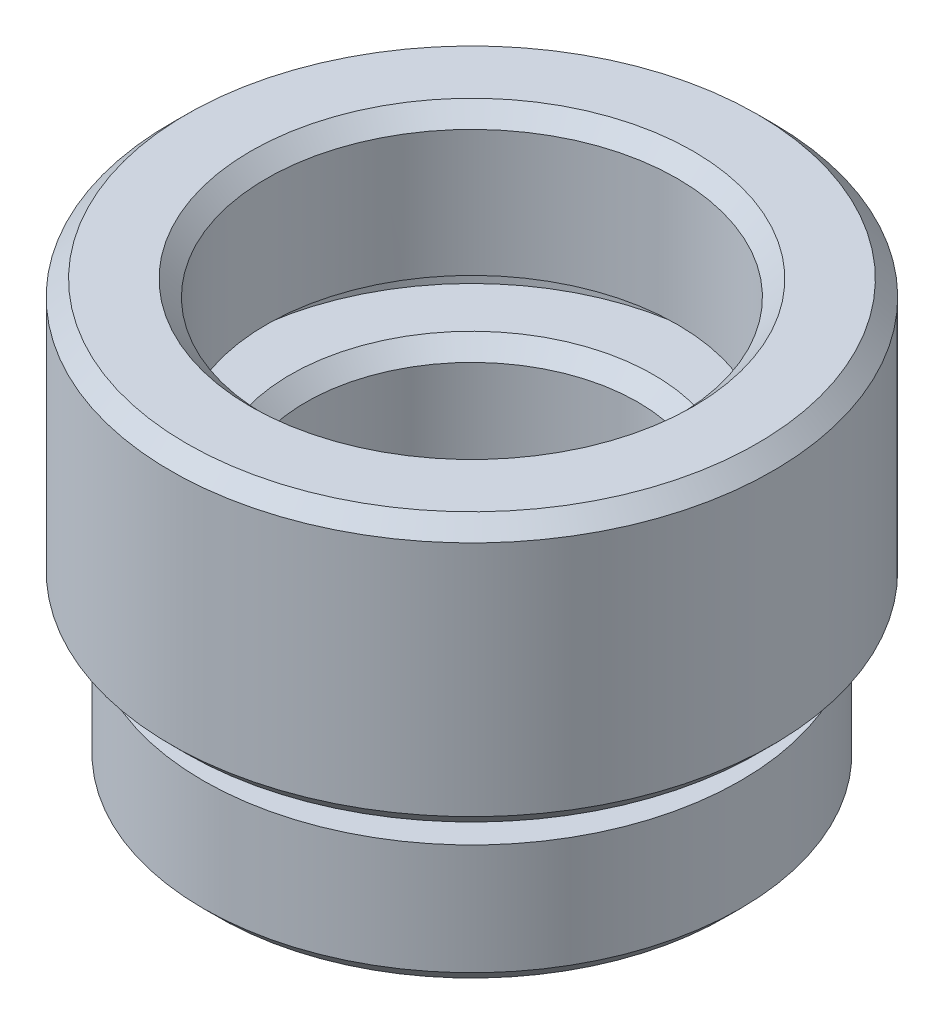
SolidWorks part; units mm, degrees
ref_plane "前视基准面" through (0, 0, 0) normal (0, 0, 1) x (1, 0, 0)
ref_plane "上视基准面" through (0, 0, 0) normal (0, 1, 0) x (1, 0, 0)
ref_plane "右视基准面" through (0, 0, 0) normal (1, 0, 0) x (0, 0, -1)
sketch "草图1" plane through (0, 0, 0) normal (0, 0, 1) x (1, 0, 0)
  line L0 (0, 0) -> (0, 51.3875) construction
  line L1 (4.5, 0) -> (4.5, 2)
  line L2 (4.5, 2) -> (5, 2)
  line L3 (5, 2) -> (5, 3.5)
  line L4 (5, 3.5) -> (6.35, 3.5)
  line L5 (6.35, 3.5) -> (6.35, 4.5)
  line L6 (6.35, 4.5) -> (5.25, 4.5)
  line L7 (5.25, 4.5) -> (5.25, 8)
  line L8 (5.25, 8) -> (7.6, 8)
  line L9 (4.5, 0) -> (8, 0)
  line L10 (7.6, 8) -> (7.6, 9)
  line L11 (7.6, 9) -> (6.5, 9)
  line L12 (6.5, 9) -> (6.5, 13.5)
  line L13 (6.5, 13.5) -> (9.025, 13.5)
  line L14 (0, 0) -> (5.8539, 0) construction
  line L15 (8.5, 0.5) -> (8.5, 4)
  line L16 (8.5, 4) -> (7, 4)
  line L17 (7, 4) -> (7, 5)
  line L18 (7, 5) -> (9.025, 5)
  line L19 (9.525, 5.5) -> (9.525, 13)
  line L20 (8, 0) -> (8.5, 0.5)
  line L21 (9.025, 5) -> (9.525, 5.5)
  line L22 (9.525, 13) -> (9.025, 13.5)
  point P13 (8.5, 0)
  point P22 (9.525, 5)
  point P24 (9.525, 13.5)
  dimension "D1" = 4.5
  dimension "D2" = 2
  dimension "D3" = 5
  dimension "D4" = 1.5
  dimension "D5" = 6.35
  dimension "D6" = 1
  dimension "D7" = 5.25
  dimension "D8" = 1
  dimension "D9" = 7.6
  dimension "D10" = 5.5
  dimension "D11" = 13.5
  dimension "D12" = 6.5
  dimension "D13" = 8.5
  dimension "D14" = 1
  dimension "D15" = 0.5
  dimension "D16" = 7
  dimension "D17" = 9.525
  dimension "D18" = 0.5
  dimension "D19" = 45
  dimension "D20" = 45
  dimension "D21" = 0.5
  dimension "D22" = 45
  dimension "D23" = 5
revolve "旋转1" add sketch "草图1" angle 360 about L0
cosmetic thread "装饰螺纹线1"
cosmetic thread "装饰螺纹线2"
cosmetic thread "装饰螺纹线3"
chamfer "倒角1" distance 0.5 angle 45 2 edges at (0, 8, -5.25) (0, 13.5, -6.5)
